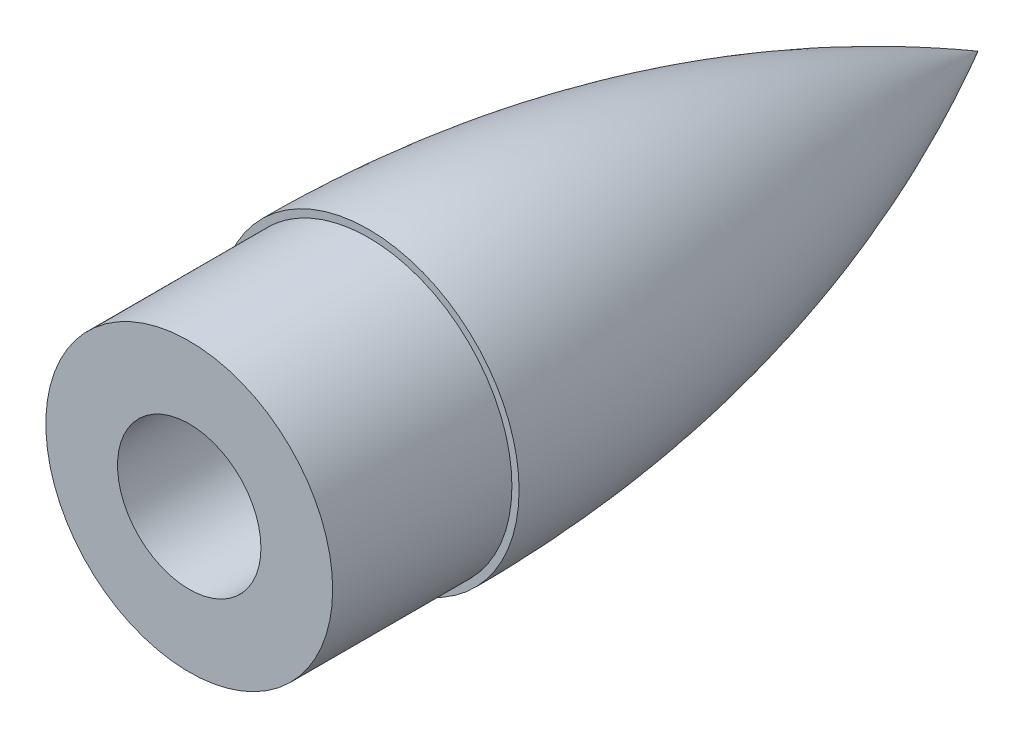
SolidWorks part; units mm, degrees
material "ABS"
ref_plane "Front Plane" through (0, 0, 0) normal (0, 0, 1) x (1, 0, 0)
ref_plane "Top Plane" through (0, 0, 0) normal (0, 1, 0) x (1, 0, 0)
ref_plane "Right Plane" through (0, 0, 0) normal (1, 0, 0) x (0, 0, -1)
sketch "Sketch1" plane through (0, 0, 0) normal (1, 0, 0) x (0, 0, -1)
  line L0 (-168, 0) -> (168, 0) construction
  line L1 (0, -42) -> (0, 42) construction
  line L2 (73.7564, 42) -> (-73.7564, 42) construction
  line L3 (72.8044, 40) -> (-72.8044, 40) construction
  line L4 (0, 40) -> (0, 42)
  line L5 (0, -40) -> (0, -42)
  line L6 (65.4024, 0) -> (-37.1775, 0)
  line L7 (168, 0) -> (170, 0)
  line L8 (0, 40) -> (23.6262, 40) construction
  spline S0 degree 2 poles (0, 42) (92.1954, 42) (170, 0) knots 0 0 0 1 1 1
  spline S1 degree 2 poles (0, -42) (92.1954, -42) (170, 0) knots 0 0 0 1 1 1
  spline S2 degree 2 poles (0, 40) (91.0055, 40) (168, 0) knots 0 0 0 1 1 1
  spline S3 degree 2 poles (0, -40) (91.0055, -40) (168, 0) knots 0 0 0 1 1 1
  point P0 (0, 40)
  point P4 (0, 0)
  point P7 (0, 0)
  point P9 (168, 0)
  dimension "D1" = 84
  dimension "D2" = 170
  dimension "D3" = 80
  dimension "D4" = 2
revolve "Revolve6" add sketch "Sketch1" angle 360 about L0
sketch "Sketch2" [suppressed] plane through (0, 0, 0) normal (0, 0, 1) x (1, 0, 0)
  circle A0 centre (0, 0) radius 42 construction
  circle A3 centre (0, 0) radius 42
sketch "Sketch15" plane through (0, 0, 0) normal (1, 0, 0) x (0, 0, -1)
  line L3 (65.4024, 0) -> (-37.1775, 0) construction
  line L6 (0, 40) -> (0, 0)
  line L7 (168, 0) -> (0, 0)
  parabola Q1 (0, 40) -> (168, 0) focus (64.5986, -144.4227) apex (122.1376, 19.8455) construction
  parabola Q5 (0, 40) -> (168, 0) focus (64.5986, -144.4227) apex (122.1376, 19.8455)
  point P1 (60.2618, 0)
revolve "Revolve7" add sketch "Sketch15" angle 360 about L7
sketch "Sketch16" plane through (0, 0, 0) normal (1, 0, 0) x (0, 0, -1)
  line L0 (168, 0) -> (0, 0) construction
  line L1 (0, 40) -> (0, 0) construction
  line L2 (85, 0) -> (0, 0)
  line L3 (0, 40) -> (0, 0)
  line L4 (85, 30.5863) -> (85, 0)
  parabola Q0 (0, 40) -> (168, 0) focus (64.5986, -144.4227) apex (122.1376, 19.8455) construction
  parabola Q1 (0, 40) -> (85, 30.5863) focus (64.5986, -144.4227) apex (122.1376, 19.8455)
  dimension "D1" = 85
revolve "Cut-Revolve1" cut sketch "Sketch16" angle 360 about L2
sketch "Sketch18" plane through (0, 0, -85) normal (0, 0, 1) x (1, 0, 0)
  line L0 (0, -18) -> (0, 18) construction
  line L1 (-4.2842, 0) -> (4.2842, 0) construction
  line L2 (-10, 24) -> (10, 24)
  line L3 (-10, 24) -> (-10, 12)
  line L4 (-10, 12) -> (10, 12)
  line L5 (10, 24) -> (10, 12)
  line L6 (-10, 24) -> (10, 12) construction
  line L7 (-10, 12) -> (10, 24) construction
  line L8 (-10, -12) -> (10, -12)
  line L9 (10, -24) -> (10, -12)
  line L10 (-10, -24) -> (-10, -12)
  line L11 (-10, -24) -> (10, -24)
  circle A1 centre (0, 18) radius 5 construction
  circle A2 centre (-8, 18) radius 1.5 construction
  circle A3 centre (8, 18) radius 1.5 construction
  circle A4 centre (0, -18) radius 5 construction
  circle A5 centre (8, -18) radius 1.5 construction
  circle A6 centre (-8, -18) radius 1.5 construction
  point P0 (0, 0)
  point P12 (0, 0)
  dimension "D1" = 36
  dimension "D3" = 3
  dimension "D2" = 20
  dimension "D4" = 8
extrude "Boss-Extrude2" add sketch "Sketch18" along normal blind 10
sketch "Sketch19" plane through (0, 0, -75) normal (0, 0, 1) x (1, 0, 0)
  line L4 (10, 12) -> (10, 24)
  line L5 (10, 24) -> (-10, 24)
  line L6 (-10, 24) -> (-10, 12)
  line L7 (-10, 12) -> (10, 12)
  line L8 (10, 12) -> (10, 24)
  line L9 (10, 24) -> (-10, 24)
  line L10 (-10, 24) -> (-10, 12)
  line L11 (-10, 12) -> (10, 12)
  circle A0 centre (8, -18) radius 1.5 construction
  circle A1 centre (-8, -18) radius 1.5 construction
  circle A2 centre (8, 18) radius 1.5 construction
  circle A3 centre (-8, 18) radius 1.5 construction
  circle A4 centre (8, -18) radius 1.5
  circle A5 centre (-8, -18) radius 1.5
  circle A6 centre (8, 18) radius 1.5
  circle A7 centre (-8, 18) radius 1.5
  dimension "D1" = 0
extrude "Cut-Extrude1" cut sketch "Sketch19" against normal blind 15 contours A7 | A6 | A5 | A4
sketch "Sketch20" plane through (0, 0, -75) normal (0, 0, 1) x (1, 0, 0)
  circle A0 centre (0, 18) radius 5 construction
  circle A1 centre (0, 18) radius 5
  circle A2 centre (0, -18) radius 5 construction
  circle A3 centre (0, -18) radius 5
sketch "Sketch22" plane through (0, 0, 0) normal (1, 0, 0) x (0, 0, -1)
  line L0 (75, 23) -> (75, 13) construction
  line L1 (75, -13) -> (75, -23) construction
  arc A0 (75, 18) -> (75, -18) centre (77.6352, 0) ccw
sweep "Sweep2" add path "Sketch22" circular profile diameter 10 parameters "D3"=10
sketch "Sketch30" plane through (0, 0, -85) normal (0, 0, 1) x (1, 0, 0)
  circle A1 centre (0, 0) radius 30.5863
  circle A5 centre (0, 0) radius 30.5863
  dimension "D1" = 0
extrude "Cut-Extrude2" [suppressed] cut sketch "Sketch30" along normal blind 76
sketch "Sketch43" plane through (0, 0, 0) normal (1, 0, 0) x (0, 0, -1)
  line L0 (65.4024, 0) -> (-37.1775, 0) construction
  line L1 (30, 0) -> (0, 0)
  line L2 (0, -42) -> (0, 42) construction
  line L3 (0, 0) -> (0, 40)
  line L4 (30, 0) -> (30, 38.8848)
  parabola Q0 (0, 40) -> (168, 0) focus (64.5986, -144.4227) apex (122.1376, 19.8455) construction
  parabola Q1 (0, 40) -> (30, 38.8848) focus (64.5986, -144.4227) apex (122.1376, 19.8455)
  dimension "D1" = 30
revolve "Revolve8" add sketch "Sketch43" angle 360 about L1
sketch "Sketch46" plane through (0, 0, 0) normal (0, 0, 1) x (1, 0, 0)
  circle A1 centre (0, 0) radius 40
  circle A2 centre (0, 0) radius 40
  dimension "D1" = 0
extrude "Boss-Extrude4" add sketch "Sketch46" along normal blind 50 separate body
sketch "Sketch47" plane through (0, 0, 50) normal (0, 0, 1) x (1, 0, 0)
  circle A0 centre (0, 0) radius 20
  circle A1 centre (0, 0) radius 40 construction
  dimension "D1" = 20
extrude "Cut-Extrude3" cut sketch "Sketch47" against normal up to surface (80 mm away)
